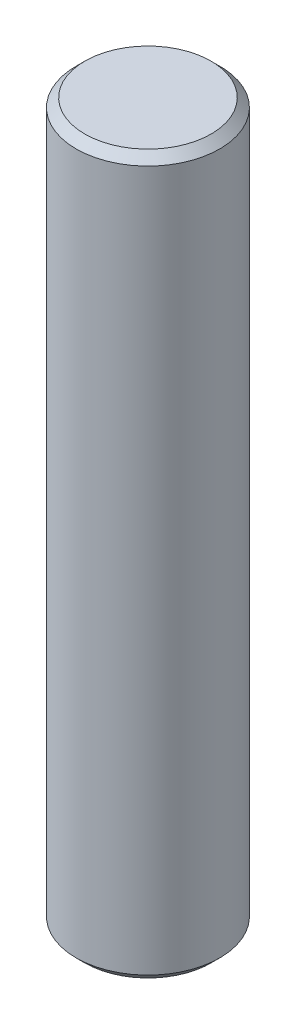
SolidWorks part; units mm, degrees
ref_plane "Front Plane" through (0, 0, 0) normal (0, 0, 1) x (1, 0, 0)
ref_plane "Top Plane" through (0, 0, 0) normal (0, 1, 0) x (1, 0, 0)
ref_plane "Right Plane" through (0, 0, 0) normal (1, 0, 0) x (0, 0, -1)
sketch "Sketch1" plane through (0, 0, 0) normal (0, 1, 0) x (1, 0, 0)
  circle A0 centre (0, 0) radius 6.35
  dimension "D1" = 12.7
extrude "Boss-Extrude1" add sketch "Sketch1" along normal blind 63.5
chamfer "Chamfer1" distance 0.762 angle 45 2 edges at (0, 63.5, 6.35) (0, 0, 6.35)
